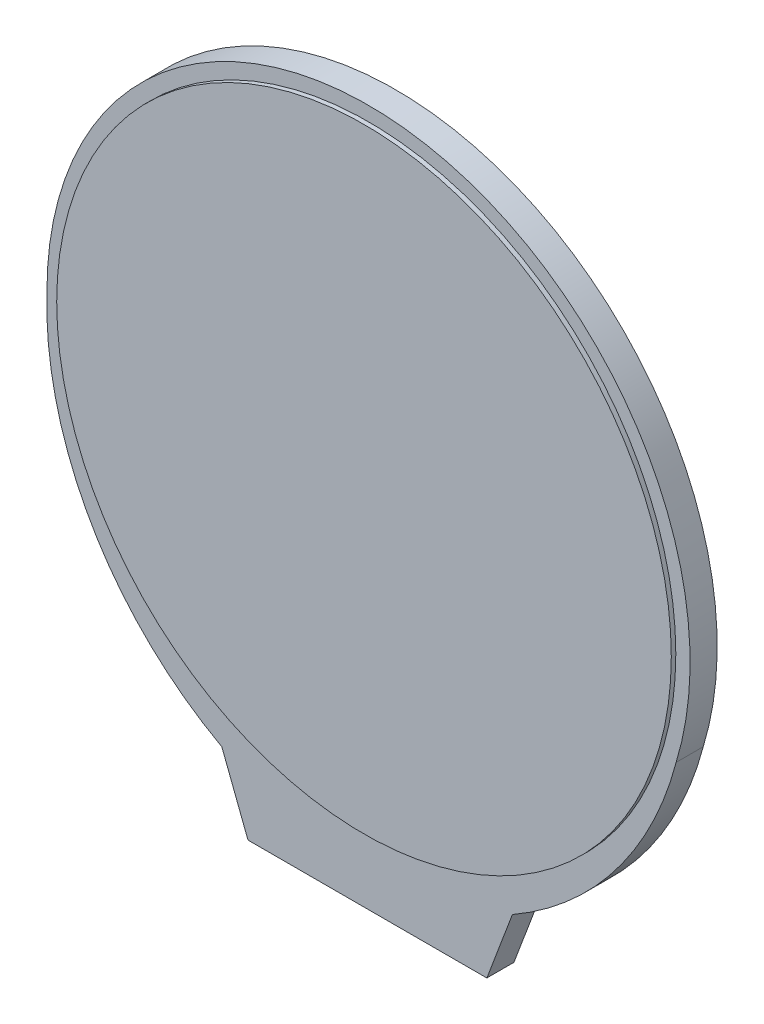
SolidWorks part; units mm, degrees
material "Plastique personnalisé"
ref_plane "Plan de face" through (0, 0, 0) normal (0, 0, 1) x (1, 0, 0)
ref_plane "Plan de dessus" through (0, 0, 0) normal (0, 1, 0) x (1, 0, 0)
ref_plane "Plan de droite" through (0, 0, 0) normal (1, 0, 0) x (0, 0, -1)
sketch "Esquisse5" plane through (0, 0, 0) normal (0, 0, 1) x (1, 0, 0)
  line L0 (-18.4506, -2.6277) -> (17.1494, -2.6277) construction
  line L1 (-17.7221, 5.2513) -> (17.8739, 5.2513) construction
  line L2 (-6.5956, -15.5109) -> (-7.5119, -13.1563)
  line L3 (-6.5956, -15.5109) -> (6.6261, -15.5109)
  line L4 (6.6261, -15.5109) -> (7.5593, -13.1128)
  arc A0 (16.6123, -1.3357) -> (-17.7221, 4.9857) centre (0.0759, 5.2513) ccw
  arc A1 (-9.3341, -10.8525) -> (-17.7221, 5.2513) centre (1.6717, 5.1165) cw
  arc A2 (9.3221, -10.8507) -> (16.6123, -1.3357) centre (-0.3842, 4.1364) ccw
  arc A3 (-7.5119, -13.1563) -> (-9.3341, -10.8525) centre (-12.1715, -14.9695) ccw
  arc A4 (7.5593, -13.1128) -> (9.3221, -10.8507) centre (12.2189, -14.926) cw
  dimension "D2" = 5
  dimension "D1" = 35.6
sketch "languette" plane through (0, 0, 0) normal (0, 0, 1) x (1, 0, 0)
  line L0 (-6.5956, -8.8887) -> (-5.6154, -7.489)
  line L1 (-6.5956, -15.5109) -> (5.9034, -15.5109)
  line L2 (-6.5956, -15.5109) -> (-6.5956, -8.8887)
  line L3 (-5.1154, -4.8839) -> (5.4034, -4.8839)
  line L4 (5.9034, -15.5109) -> (5.9034, -5.3839)
  line L5 (-5.6154, -7.489) -> (-5.6154, -5.3839)
  arc A0 (5.4034, -4.8839) -> (5.9034, -5.3839) centre (5.4034, -5.3839) cw
  arc A1 (-5.6154, -5.3839) -> (-5.1154, -4.8839) centre (-5.1154, -5.3839) cw
  circle A2 centre (-5.2363, -9.19) radius 0.598
  circle A3 centre (4.7369, -9.19) radius 0.6027
  dimension "D1" = 0.5
  dimension "D2" = 0.5
sketch "contacts" plane through (0, 0, 0) normal (0, 0, 1) x (1, 0, 0)
  line L0 (-5.1154, -4.8839) -> (5.4034, -4.8839) construction
  line L1 (-4.0115, -7.0029) -> (4.2995, -7.0029)
  line L2 (-4.0115, -7.0029) -> (-4.0115, -4.8839)
  line L3 (-4.0115, -4.8839) -> (4.2995, -4.8839)
  line L4 (4.2995, -7.0029) -> (4.2995, -4.8839)
extrude "Boss.-Extru.1" add sketch "languette" against normal blind 0.25
extrude "Boss.-Extru.2" add sketch "contacts" against normal blind 0.26
sketch "Esquisse6" plane through (0, 0, 0) normal (0, 0, 1) x (1, 0, 0)
  line L0 (-6.5956, -15.5109) -> (-8.0437, -11.7619)
  line L1 (6.6261, -15.5109) -> (8.0394, -11.7619)
  line L2 (6.6261, -15.5109) -> (-6.5956, -15.5109)
  arc A0 (17.1033, 0.0638) -> (-17.724, 5.1963) centre (0.0759, 5.2513) ccw
  arc A1 (-17.724, 5.1963) -> (-8.0437, -11.7619) centre (0.8774, 4.5726) ccw
  arc A2 (17.1033, 0.0638) -> (8.0394, -11.7619) centre (-1.5234, 4.954) cw
extrude "Boss.-Extru.3" add sketch "Esquisse6" along normal blind 1.5
sketch "Esquisse7" plane through (0, 0, 1.5) normal (0, 0, 1) x (1, 0, 0)
  circle A0 centre (0.0759, 5.2513) radius 17.0106
extrude "Boss.-Extru.4" add sketch "Esquisse7" along normal blind 0.25
